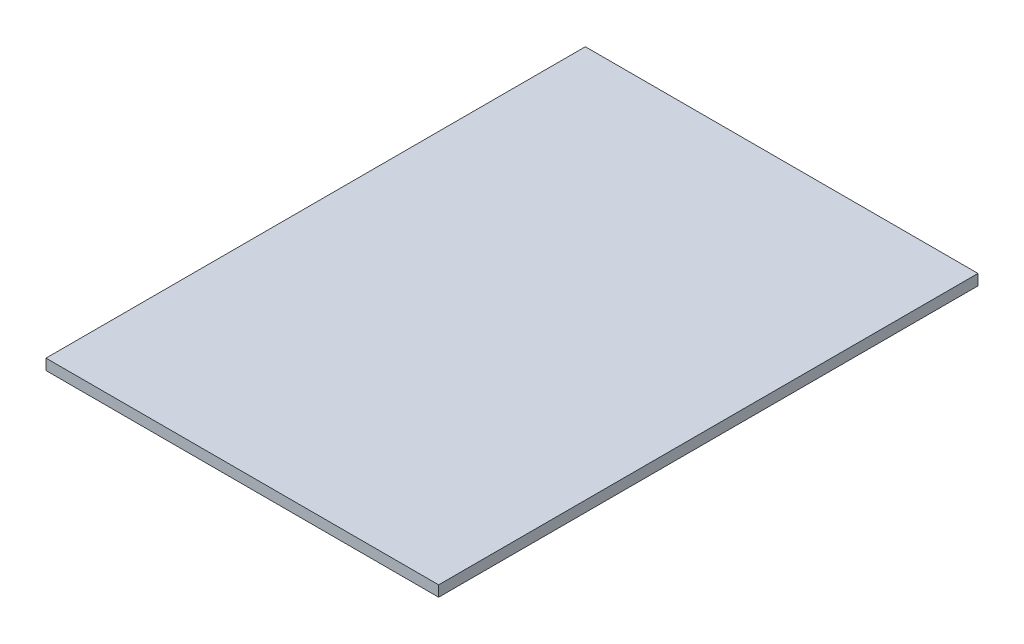
SolidWorks part; units mm, degrees
ref_plane "Front Plane" through (0, 0, 0) normal (0, 0, 1) x (1, 0, 0)
ref_plane "Top Plane" through (0, 0, 0) normal (0, 1, 0) x (1, 0, 0)
ref_plane "Right Plane" through (0, 0, 0) normal (1, 0, 0) x (0, 0, -1)
sketch "Sketch1" plane through (0, 0, 0) normal (0, 1, 0) x (1, 0, 0)
  line L1 (-1.82, 2.5) -> (1.82, 2.5)
  line L2 (-1.82, 2.5) -> (-1.82, -2.5)
  line L3 (-1.82, -2.5) -> (1.82, -2.5)
  line L4 (1.82, 2.5) -> (1.82, -2.5)
  line L5 (-1.82, 2.5) -> (1.82, -2.5) construction
  line L6 (-1.82, -2.5) -> (1.82, 2.5) construction
  point P0 (0, 0)
  dimension "D1" = 3.64
  dimension "D2" = 5
extrude "Boss-Extrude1" add sketch "Sketch1" along normal blind 0.1
